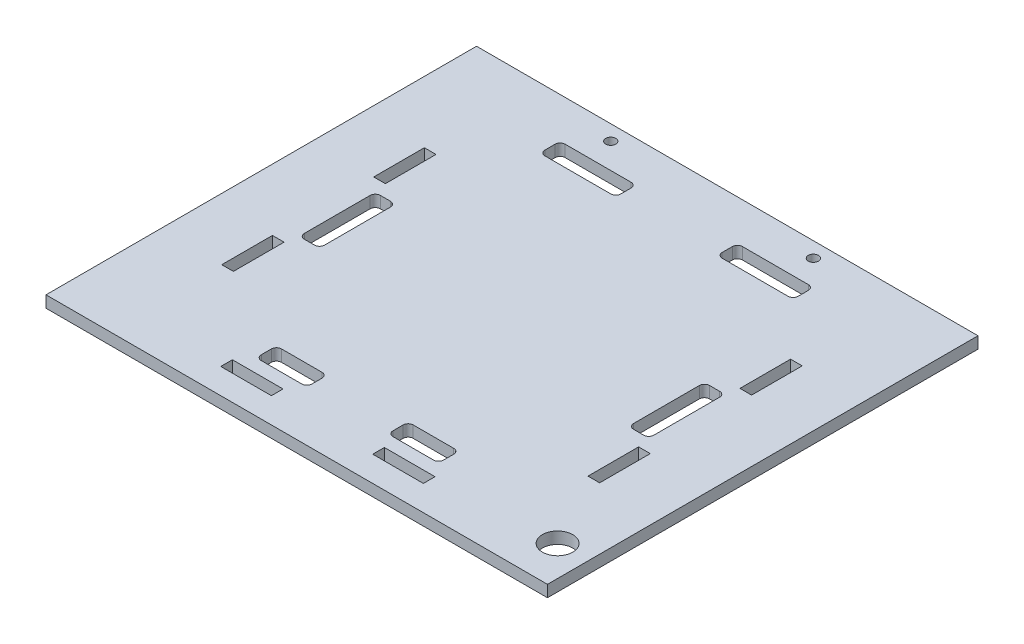
SolidWorks part; units mm, degrees
ref_plane "Front Plane" through (0, 0, 0) normal (0, 0, 1) x (1, 0, 0)
ref_plane "Top Plane" through (0, 0, 0) normal (0, 1, 0) x (1, 0, 0)
ref_plane "Right Plane" through (0, 0, 0) normal (1, 0, 0) x (0, 0, -1)
sketch "Sketch1" plane through (0, 0, 0) normal (0, 1, 0) x (1, 0, 0)
  line L0 (0, 0) -> (-49.5, 0) construction
  line L1 (0, 0) -> (49.5, 0) construction
  line L2 (0, 0) -> (0, -50) construction
  line L3 (0, 0) -> (0, 35) construction
  line L4 (0, -50) -> (-49.5, -50)
  line L5 (-49.5, -50) -> (-49.5, 0)
  line L6 (-49.5, 0) -> (-49.5, 35)
  line L7 (-49.5, 35) -> (0, 35)
  line L8 (0, 35) -> (49.5, 35)
  line L9 (49.5, 35) -> (49.5, 0)
  line L10 (49.5, 0) -> (49.5, -50)
  line L11 (49.5, -50) -> (0, -50)
  dimension "D1" = 49.5
  dimension "D2" = 49.5
  dimension "D3" = 50
  dimension "D4" = 35
extrude "Boss-Extrude1" add sketch "Sketch1" along normal blind 2.3
sketch "Sketch2" plane through (0, 2.3, 0) normal (0, 1, 0) x (1, 0, 0)
  line L0 (-49.5, 35) -> (-49.5, 32) construction
  line L1 (-49.5, 35) -> (-49.5, -50) construction
  line L2 (49.5, 35) -> (-49.5, 35) construction
  line L3 (-49.5, 32) -> (49.5, 32) construction
  line L4 (49.5, -50) -> (49.5, 35) construction
  line L5 (0, 32) -> (-20, 32) construction
  line L6 (0, 32) -> (20, 32) construction
  circle A0 centre (-20, 32) radius 1
  circle A1 centre (20, 32) radius 1
  dimension "D4" = 2
  dimension "D1" = 3
  dimension "D2" = 20
  dimension "D3" = 20
extrude "Cut-Extrude1" cut sketch "Sketch2" against normal blind 2.3
sketch "Sketch3" plane through (0, 2.3, 0) normal (0, 1, 0) x (1, 0, 0)
  line L0 (-49.5, -50) -> (-49.5, -45) construction
  line L1 (-49.5, 35) -> (-49.5, -50) construction
  line L2 (-49.5, -45) -> (49.5, -45) construction
  line L3 (49.5, -50) -> (49.5, 35) construction
  line L4 (-49.5, -45) -> (-49.5, -42.7) construction
  line L5 (-49.5, -42.7) -> (49.5, -42.7) construction
  line L6 (0, -45) -> (-10, -45) construction
  line L7 (0, -45) -> (10, -45) construction
  line L8 (-10, -45) -> (-20, -45)
  line L9 (10, -45) -> (20, -45)
  line L10 (-20, -45) -> (-20, -42.7)
  line L11 (-20, -42.7) -> (-10, -42.7)
  line L12 (-10, -42.7) -> (-10, -45)
  line L13 (10, -45) -> (10, -42.7)
  line L14 (10, -42.7) -> (20, -42.7)
  line L15 (20, -42.7) -> (20, -45)
  dimension "D1" = 5
  dimension "D2" = 2.3
  dimension "D3" = 10
  dimension "D4" = 10
  dimension "D5" = 10
  dimension "D6" = 10
extrude "Cut-Extrude2" cut sketch "Sketch3" against normal blind 2.3
sketch "Sketch4" plane through (0, 2.3, 0) normal (0, 1, 0) x (1, 0, 0)
  line L0 (0, 35) -> (0, 27) construction
  line L1 (49.5, 35) -> (-49.5, 35) construction
  line L2 (0, 27) -> (-10, 27) construction
  line L3 (0, 27) -> (10, 27) construction
  line L4 (-10, 27) -> (-25, 27)
  line L5 (10, 27) -> (25, 27)
  line L6 (-25, 27) -> (-25, 23)
  line L7 (-25, 23) -> (25, 23) construction
  line L8 (25, 23) -> (25, 27)
  line L9 (-10, 27) -> (-10, 23)
  line L10 (10, 27) -> (10, 23)
  line L11 (10, 23) -> (25, 23)
  line L12 (-10, 23) -> (-25, 23)
  dimension "D1" = 8
  dimension "D2" = 10
  dimension "D3" = 10
  dimension "D4" = 15
  dimension "D5" = 15
  dimension "D6" = 4
extrude "Cut-Extrude3" cut sketch "Sketch4" against normal blind 10
sketch "Sketch5" plane through (0, 2.3, 0) normal (0, 1, 0) x (1, 0, 0)
  line L0 (0, -50) -> (-35, -50) construction
  line L1 (-49.5, -50) -> (49.5, -50) construction
  line L2 (0, -50) -> (35, -50) construction
  line L3 (-35, -50) -> (-35, 35) construction
  line L4 (49.5, 35) -> (-49.5, 35) construction
  line L5 (35, -50) -> (35, 35) construction
  line L6 (-35, -50) -> (-37.3, -50) construction
  line L7 (35, -50) -> (37.3, -50) construction
  line L8 (37.3, -50) -> (37.3, 35) construction
  line L9 (-37.3, -50) -> (-37.3, 35) construction
  line L10 (-35, -7.5) -> (-35, -17.5) construction
  line L11 (-35, -7.5) -> (-35, 2.5) construction
  line L12 (-35, 2.5) -> (-35, 12.5)
  line L13 (-35, -17.5) -> (-35, -27.5)
  line L14 (-35, 2.5) -> (35, 2.5) construction
  line L15 (-35, 12.5) -> (35, 12.5) construction
  line L16 (-35, -17.5) -> (35, -17.5) construction
  line L17 (-35, -27.5) -> (35, -27.5) construction
  line L18 (-35, 12.5) -> (-37.3, 12.5)
  line L19 (-37.3, 12.5) -> (-37.3, 2.5)
  line L20 (-37.3, 2.5) -> (-35, 2.5)
  line L21 (35, -17.5) -> (37.3, -17.5)
  line L22 (-35, -17.5) -> (-37.3, -17.5)
  line L23 (-37.3, -17.5) -> (-37.3, -27.5)
  line L24 (-37.3, -27.5) -> (-35, -27.5)
  line L25 (35, 2.5) -> (35, 12.5)
  line L26 (35, 12.5) -> (37.3, 12.5)
  line L27 (37.3, 12.5) -> (37.3, 2.5)
  line L28 (37.3, 2.5) -> (35, 2.5)
  line L29 (37.3, -17.5) -> (37.3, -27.5)
  line L30 (37.3, -27.5) -> (35, -27.5)
  line L31 (35, -27.5) -> (35, -17.5)
  dimension "D1" = 35
  dimension "D2" = 35
  dimension "D3" = 2.3
  dimension "D4" = 2.3
  dimension "D5" = 10
  dimension "D6" = 10
  dimension "D7" = 10
  dimension "D8" = 10
extrude "Cut-Extrude4" cut sketch "Sketch5" against normal blind 2.3
fillet "Fillet1" radius 1 8 edges at (25, 1.15, -23) (10, 1.15, -23) (25, 1.15, -27) (10, 1.15, -27) (-10, 1.15, -23) (-25, 1.15, -23) (-10, 1.15, -27) (-25, 1.15, -27)
sketch "Sketch6" plane through (0, 2.3, 0) normal (0, 1, 0) x (1, 0, 0)
  line L0 (49.5, -50) -> (34.5, -50) construction
  line L1 (-49.5, -50) -> (49.5, -50) construction
  line L2 (34.5, -50) -> (34.5, -15) construction
  line L3 (34.5, -15) -> (34.5, 0)
  line L4 (34.5, 0) -> (30.5, 0)
  line L5 (30.5, 0) -> (30.5, -15)
  line L6 (30.5, -15) -> (34.5, -15)
  line L7 (-49.5, -50) -> (-34.5, -50) construction
  line L8 (-34.5, -50) -> (-34.5, -15) construction
  line L9 (-34.5, -15) -> (-30.5, -15)
  line L10 (-34.5, -15) -> (-34.5, 0)
  line L11 (-34.5, 0) -> (-30.5, 0)
  line L12 (-30.5, 0) -> (-30.5, -15)
  line L13 (0, -50) -> (0, -40) construction
  line L14 (0, -40) -> (-8, -40) construction
  line L15 (0, -40) -> (8, -40) construction
  line L16 (-8, -40) -> (-18, -40)
  line L17 (8, -40) -> (18, -40)
  line L18 (-18, -40) -> (-18, -36)
  line L19 (-18, -36) -> (18, -36) construction
  line L20 (18, -40) -> (18, -36)
  line L21 (8, -40) -> (8, -36)
  line L22 (8, -36) -> (18, -36)
  line L23 (-18, -36) -> (-8, -36)
  line L24 (-8, -36) -> (-8, -40)
  dimension "D1" = 15
  dimension "D2" = 35
  dimension "D3" = 15
  dimension "D4" = 4
  dimension "D5" = 15
  dimension "D6" = 35
  dimension "D7" = 4
  dimension "D8" = 15
  dimension "D9" = 10
  dimension "D10" = 8
  dimension "D11" = 8
  dimension "D12" = 10
  dimension "D13" = 10
  dimension "D14" = 4
extrude "Cut-Extrude5" cut sketch "Sketch6" against normal blind 10
fillet "Fillet3" radius 1 16 edges at (34.5, 1.15, 0) (30.5, 1.15, 0) (34.5, 1.15, 15) (30.5, 1.15, 15) (-30.5, 1.15, 15) (-30.5, 1.15, 0) (-34.5, 1.15, 15) (-34.5, 1.15, 0) (8, 1.15, 40) (18, 1.15, 40) (18, 1.15, 36) (8, 1.15, 36) (-8, 1.15, 40) (-8, 1.15, 36) (-18, 1.15, 40) (-18, 1.15, 36)
sketch "Sketch7" plane through (0, 2.3, 0) normal (0, 1, 0) x (1, 0, 0)
  line L0 (49.5, -50) -> (43.5, -50) construction
  line L1 (-49.5, -50) -> (49.5, -50) construction
  line L2 (43.5, -50) -> (43.5, -42) construction
  circle A0 centre (43.5, -42) radius 3
  dimension "D3" = 6
  dimension "D1" = 6
  dimension "D2" = 8
extrude "Cut-Extrude6" cut sketch "Sketch7" against normal blind 10
